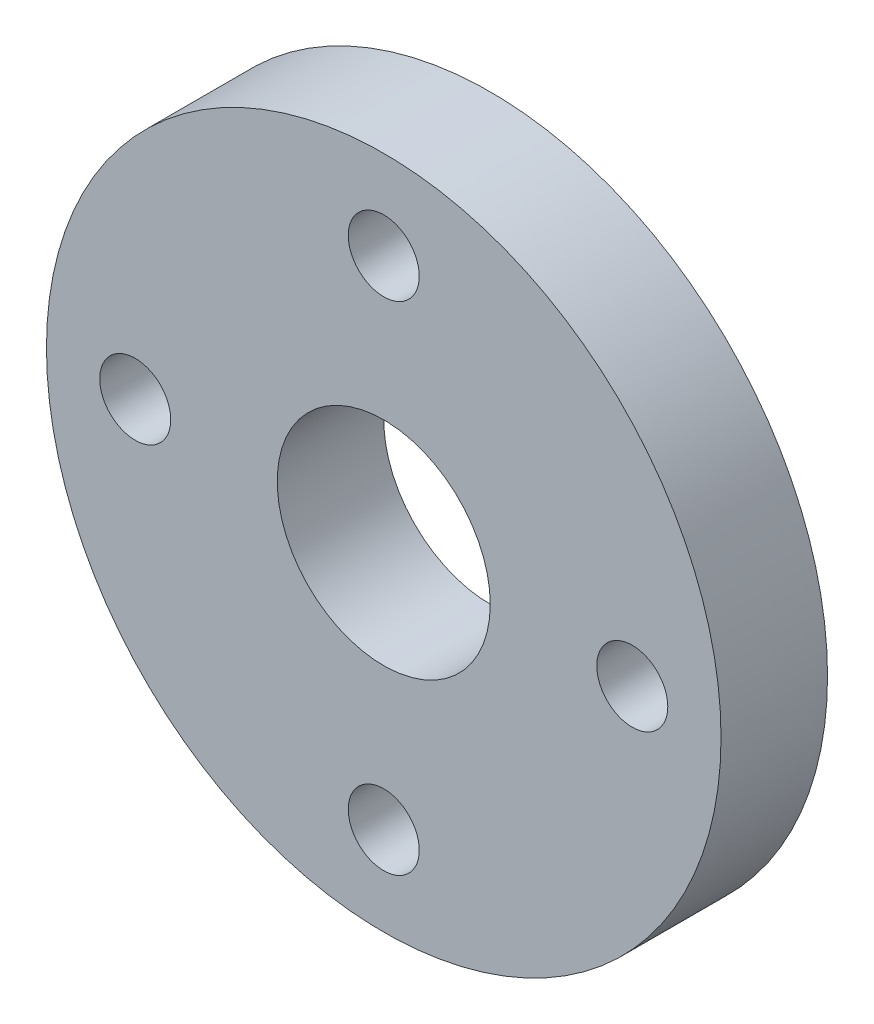
SolidWorks part; units mm, degrees
ref_plane "Front Plane" through (0, 0, 0) normal (0, 0, 1) x (1, 0, 0)
ref_plane "Top Plane" through (0, 0, 0) normal (0, 1, 0) x (1, 0, 0)
ref_plane "Right Plane" through (0, 0, 0) normal (1, 0, 0) x (0, 0, -1)
sketch "Sketch1" plane through (0, 0, 0) normal (0, 0, 1) x (1, 0, 0)
  circle A0 centre (0, 0) radius 9.5
  circle A1 centre (0, 0) radius 7 construction
  circle A2 centre (0, 7) radius 1
  circle A3 centre (7, 0) radius 1
  circle A4 centre (0, -7) radius 1
  circle A5 centre (-7, 0) radius 1
  circle A6 centre (0, 0) radius 3
  dimension "D1" = 19
  dimension "D2" = 14
  dimension "D3" = 2
  dimension "D4" = 6
extrude "Boss-Extrude1" add sketch "Sketch1" along normal blind 3
